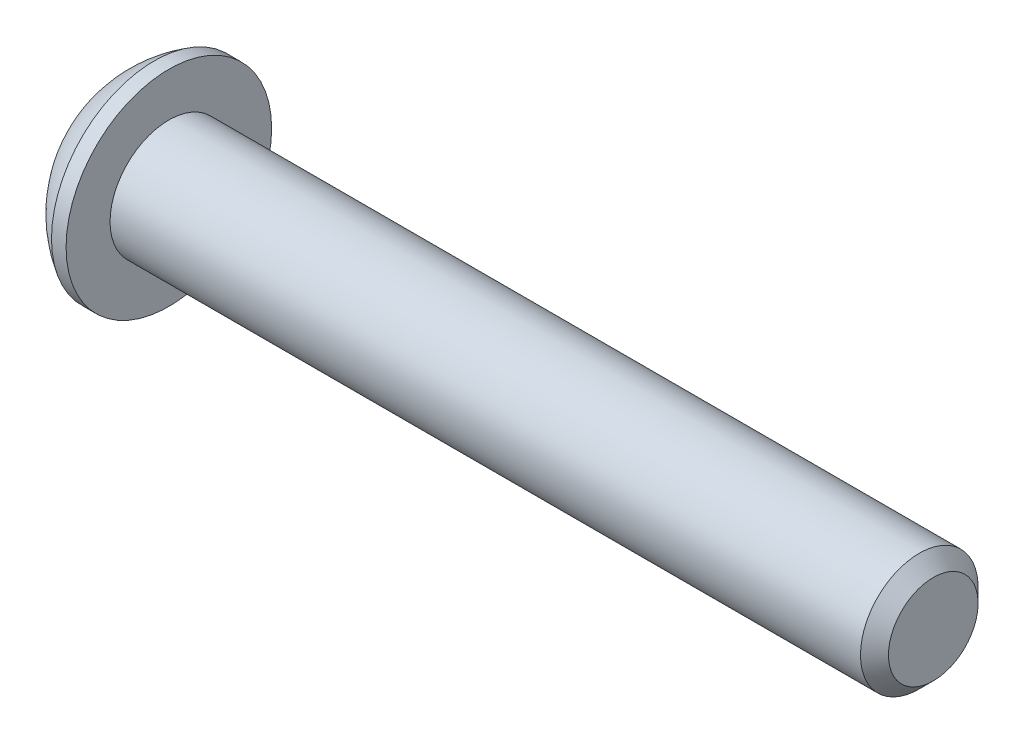
SolidWorks part; units mm, degrees
ref_plane "Plane1" through (0, 0, 0) normal (0, 0, 1) x (1, 0, 0)
ref_plane "Plane2" through (0, 0, 0) normal (0, 1, 0) x (1, 0, 0)
ref_plane "Plane3" through (0, 0, 0) normal (1, 0, 0) x (0, 0, -1)
sketch "BodySke" plane through (0, 0, 0) normal (0, 0, 1) x (1, 0, 0)
  line L0 (44.6278, 0) -> (44.6278, 2.4193)
  line L1 (43.8721, 3.175) -> (3.3528, 3.175)
  line L2 (3.3528, 3.175) -> (3.3528, 5.5499)
  line L3 (3.3528, 5.5499) -> (2.5654, 5.5499)
  line L4 (0, 0) -> (101.6, 0) construction
  line L5 (3.3528, -5.5499) -> (2.5654, -5.5499) construction
  line L6 (55.6768, -3.175) -> (3.3528, -3.175) construction
  line L7 (44.6278, 0) -> (0, 0)
  line L8 (0, 2.775) -> (0, -2.775) construction
  line L9 (0, 0) -> (0, 2.775)
  line L10 (44.6278, 2.4193) -> (43.8721, 3.175)
  line L11 (44.6278, -2.4193) -> (43.8721, -3.175) construction
  line L12 (4.6228, 9.525) -> (4.6228, -3.175) construction
  line L13 (3.3528, 9.525) -> (3.3528, -3.175) construction
  arc A1 (0, 2.775) -> (2.5654, 5.5499) centre (5.7851, 0) cw
  dimension "Diameter" = 6.35
  dimension "Head_dia" = 11.0998
  dimension "D1" = 5.5499
  dimension "Head_ht" = 3.3528
  dimension "Head_side_ht" = 0.7874
  dimension "Minor_dia" = 4.8387
  dimension "Body_ch_ang" = 45
  dimension "Advance" = 1.27
revolve "BaseBody" add sketch "BodySke" angle 360 about L4
cosmetic thread "ThreadCosmetic" [suppressed] parameters "Thread_length"=40.005, "Thread_minor"=4.8387
sketch "Sketch2" plane through (0, 0, 0) normal (0, 0, 1) x (1, 0, 0)
  line L0 (0, 1.9812) -> (2.2098, 1.9812)
  line L1 (2.2098, 1.9812) -> (3.3536, 0)
  line L3 (3.3536, 0) -> (0, 0)
  line L4 (0, 0) -> (0, 1.9812)
  line L5 (0, -1.9812) -> (2.2098, -1.9812) construction
  line L6 (0, 0) -> (47.625, 0) construction
  dimension "D2" = 60
  dimension "PreBroach_depth" = 2.2098
  dimension "PreBroach_dia" = 3.9624
revolve "PreBroach" cut sketch "Sketch2" angle 360 about L6
sketch "Sketch3" plane through (0, 0, 0) normal (1, 0, 0) x (0, 0, -1)
  line L0 (-1.9812, -1.1438) -> (-1.9812, 1.1438)
  line L1 (-1.9812, 1.1438) -> (0, 2.2877)
  line L2 (0, 2.2877) -> (1.9812, 1.1438)
  line L3 (1.9812, 1.1438) -> (1.9812, -1.1438)
  line L4 (1.9812, -1.1438) -> (0, -2.2877)
  line L5 (0, -2.2877) -> (-1.9812, -1.1438)
  dimension "Hex_size" = 3.9624
  dimension "D3" = 3.9624
  dimension "D1" = 1.9812
  dimension "D2" = 1.9812
extrude "Hex" cut sketch "Sketch3" along normal blind 2.2098
sketch "Sketch4" plane through (0, 9.525, 0) normal (1, 0, 0) x (0, 0, -1)
  line L0 (0, -9.525) -> (2.3876, -9.525)
  line L1 (0, -9.525) -> (6.1484, -5.9752) construction
  line L2 (0, -9.525) -> (1.1938, -7.4573)
  line L3 (1.9883, -8.949) -> (2.2704, -8.7861)
  line L4 (1.493, -8.0911) -> (1.7751, -7.9282)
  arc A0 (1.9883, -8.949) -> (1.493, -8.0911) centre (0, -9.525) ccw
  arc A1 (2.3876, -9.525) -> (2.2704, -8.7861) centre (0, -9.525) ccw
  arc A2 (1.1938, -7.4573) -> (1.7751, -7.9282) centre (0, -9.525) cw
  dimension "Spline_n_dim" = 4.1402
  dimension "Spline_m_dim" = 4.7752
  dimension "D1" = 30
  dimension "D2" = 60
  dimension "Spline_p_dim" = 0.9906
  dimension "D3" = 0.4953
extrude "Spline" [suppressed] cut sketch "Sketch4" along normal blind 2.2098
pattern_circular "CirPattern1" [suppressed] count 6 every 60 about axis through (0, 0, 0) along (1, 0, 0)
sketch "ThdSchSke" plane through (0, 0, 0) normal (0, 0, 1) x (1, 0, 0)
  line L0 (4.6228, -2.4193) -> (4.0937, -3.175)
  line L1 (4.6228, -2.4193) -> (5.1519, -3.175)
  line L2 (5.1519, -3.175) -> (5.1519, -3.9688)
  line L3 (-3.175, 0) -> (5.1513, 0) construction
  line L5 (5.1519, -3.9688) -> (4.0937, -3.9688)
  line L6 (4.0937, -3.9688) -> (4.0937, -3.175)
  dimension "Diameter" = 6.35
  dimension "Thread_minor" = 4.8387
  dimension "SideAngle" = 55
  dimension "VeeAngle" = 70
  dimension "Overcut" = 7.9375
  dimension "Start" = 4.6228
revolve "ThreadSchematic" [suppressed] cut sketch "ThdSchSke" angle 360 about L3
pattern_linear "ThdSchPat" [suppressed]
equation "\"D1@BodySke\" = \"Head_dia@BodySke\" * .5"
equation "\"Thread_minor@ThreadCosmetic\" = \"Minor_dia@BodySke\""
equation "\"D1@Sketch3\" = \"Hex_size@Sketch3\" / 2"
equation "\"D2@Sketch3\" = \"D1@Sketch3\""
equation "\"D3@Sketch3\" = \"Hex_size@Sketch3\""
equation "\"D3@Sketch4\" = \"Spline_p_dim@Sketch4\" / 2"
equation "\"D1@Sketch4\" = \"D2@Sketch4\" / 2"
equation "\"Thread_length@ThreadCosmetic\" = ((sgn( (\"Length@BodySke\" - \"Advance@BodySke\" ) - \"Thread_nom@BodySke\" )-1)*( (\"Length@BodySke\" - \"Advance@BodySke\" ) - \"Thread_nom@BodySke\" ))/-2+ \"Thread_nom@BodySke\""
equation "\"Thread_minor@ThdSchSke\" = \"Minor_dia@BodySke\""
equation "\"Diameter@ThdSchSke\" = \"Diameter@BodySke\""
equation "\"Overcut@ThdSchSke\" = \"Diameter@BodySke\" * 1.25"
equation "\"Start@ThdSchSke\" = \"Head_ht@BodySke\" + \"Length@BodySke\" - \"Thread_length@ThreadCosmetic\"  '---Non-countersunk---"
equation "\"Num_threads@ThdSchPat\" = int( \"Thread_length@ThreadCosmetic\" / \"Advance@BodySke\" + 0.999 )  + 1"
equation "\"Advance@ThdSchPat\" = \"Thread_length@ThreadCosmetic\" /  (\"Num_threads@ThdSchPat\" - 1) 'relax it"
equation "\"Num_threads@ThdSchPat\" = \"Num_threads@ThdSchPat\" - sgn( \"Num_threads@ThdSchPat\" - 1) '---chamfered tips only---"
